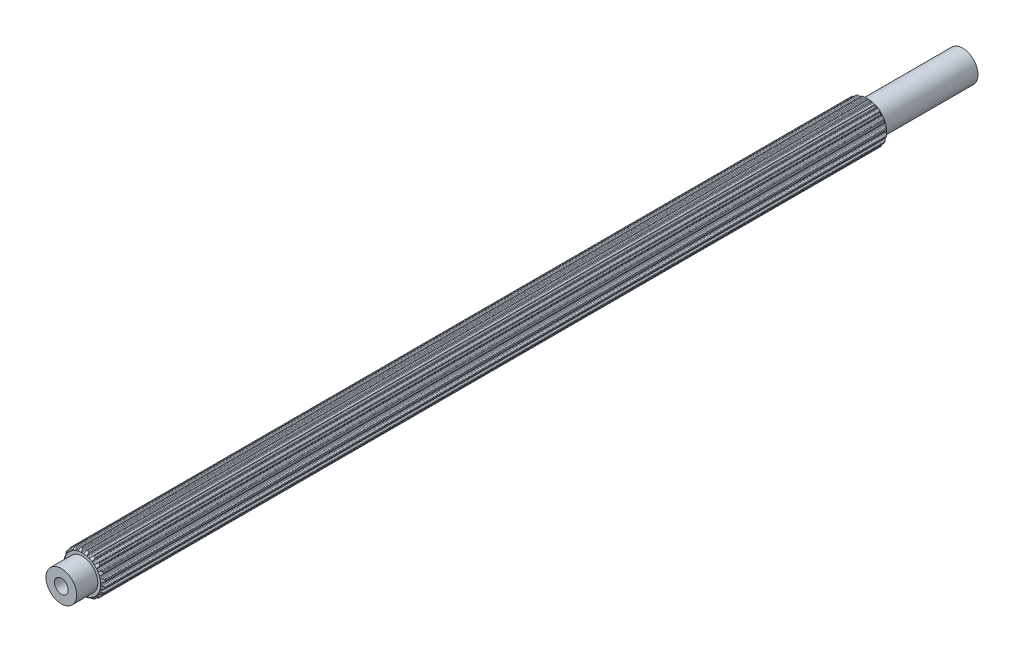
SolidWorks part; units mm, degrees
ref_plane "Front Plane" through (0, 0, 0) normal (0, 0, 1) x (1, 0, 0)
ref_plane "Top Plane" through (0, 0, 0) normal (0, 1, 0) x (1, 0, 0)
ref_plane "Right Plane" through (0, 0, 0) normal (1, 0, 0) x (0, 0, -1)
sketch "Sketch1" plane through (0, 0, 0) normal (0, 0, 1) x (1, 0, 0)
  line L0 (-0.1069, 2.9699) -> (0.1069, 2.9699)
  line L1 (0.3159, 3.2375) -> (0.2537, 3.0575)
  line L2 (-0.2964, 3.2367) -> (-0.2318, 3.0575)
  line L3 (-0.2964, 3.2367) -> (0.3159, 3.2375) construction
  line L4 (0, 3.3252) -> (0, 0) construction
  line L5 (-0.2318, 3.0575) -> (0.2537, 3.0575) construction
  line L6 (-0.4281, 3.3241) -> (0.4281, 3.3263) construction
  line L7 (0.7183, 3.1698) -> (0.7244, 2.9795)
  line L8 (0.816, 2.8576) -> (1.0195, 2.7915)
  line L9 (1.3009, 2.9815) -> (1.1862, 2.8295)
  line L10 (1.6627, 2.7927) -> (1.6097, 2.6099)
  line L11 (1.6591, 2.4655) -> (1.8322, 2.3398)
  line L12 (2.1585, 2.4335) -> (2.0025, 2.3245)
  line L13 (2.4443, 2.1423) -> (2.3374, 1.9847)
  line L14 (2.3398, 1.8322) -> (2.4655, 1.6591)
  line L15 (2.8049, 1.6474) -> (2.6228, 1.5919)
  line L16 (2.9866, 1.2821) -> (2.8363, 1.1653)
  line L17 (2.7915, 1.0195) -> (2.8576, 0.816)
  line L18 (3.1767, 0.7) -> (2.9863, 0.7035)
  line L19 (3.2367, 0.2964) -> (3.0575, 0.2318)
  line L20 (2.9699, 0.1069) -> (2.9699, -0.1069)
  line L21 (3.2375, -0.3159) -> (3.0575, -0.2537)
  line L22 (3.1698, -0.7183) -> (2.9795, -0.7244)
  line L23 (2.8576, -0.816) -> (2.7915, -1.0195)
  line L24 (2.9815, -1.3009) -> (2.8295, -1.1862)
  line L25 (2.7927, -1.6627) -> (2.6099, -1.6097)
  line L26 (2.4655, -1.6591) -> (2.3398, -1.8322)
  line L27 (2.4335, -2.1585) -> (2.3245, -2.0025)
  line L28 (2.1423, -2.4443) -> (1.9847, -2.3374)
  line L29 (1.8322, -2.3398) -> (1.6591, -2.4655)
  line L30 (1.6474, -2.8049) -> (1.5919, -2.6228)
  line L31 (1.2821, -2.9866) -> (1.1653, -2.8363)
  line L32 (1.0195, -2.7915) -> (0.816, -2.8576)
  line L33 (0.7, -3.1767) -> (0.7035, -2.9863)
  line L34 (0.2964, -3.2367) -> (0.2318, -3.0575)
  line L35 (0.1069, -2.9699) -> (-0.1069, -2.9699)
  line L36 (-0.3159, -3.2375) -> (-0.2537, -3.0575)
  line L37 (-0.7183, -3.1698) -> (-0.7244, -2.9795)
  line L38 (-0.816, -2.8576) -> (-1.0195, -2.7915)
  line L39 (-1.3009, -2.9815) -> (-1.1862, -2.8295)
  line L40 (-1.6627, -2.7927) -> (-1.6097, -2.6099)
  line L41 (-1.6591, -2.4655) -> (-1.8322, -2.3398)
  line L42 (-2.1585, -2.4335) -> (-2.0025, -2.3245)
  line L43 (-2.4443, -2.1423) -> (-2.3374, -1.9847)
  line L44 (-2.3398, -1.8322) -> (-2.4655, -1.6591)
  line L45 (-2.8049, -1.6474) -> (-2.6228, -1.5919)
  line L46 (-2.9866, -1.2821) -> (-2.8363, -1.1653)
  line L47 (-2.7915, -1.0195) -> (-2.8576, -0.816)
  line L48 (-3.1767, -0.7) -> (-2.9863, -0.7035)
  line L49 (-3.2367, -0.2964) -> (-3.0575, -0.2318)
  line L50 (-2.9699, -0.1069) -> (-2.9699, 0.1069)
  line L51 (-3.2375, 0.3159) -> (-3.0575, 0.2537)
  line L52 (-3.1698, 0.7183) -> (-2.9795, 0.7244)
  line L53 (-2.8576, 0.816) -> (-2.7915, 1.0195)
  line L54 (-2.9815, 1.3009) -> (-2.8295, 1.1862)
  line L55 (-2.7927, 1.6627) -> (-2.6099, 1.6097)
  line L56 (-2.4655, 1.6591) -> (-2.3398, 1.8322)
  line L57 (-2.4335, 2.1585) -> (-2.3245, 2.0025)
  line L58 (-2.1423, 2.4443) -> (-1.9847, 2.3374)
  line L59 (-1.8322, 2.3398) -> (-1.6591, 2.4655)
  line L60 (-1.6474, 2.8049) -> (-1.5919, 2.6228)
  line L61 (-1.2821, 2.9866) -> (-1.1653, 2.8363)
  line L62 (-1.0195, 2.7915) -> (-0.816, 2.8576)
  line L63 (-0.7, 3.1767) -> (-0.7035, 2.9863)
  line L64 (0.4281, 3.3263) -> (0.62, 3.2938)
  line L65 (1.4351, 3.0312) -> (1.6075, 2.9409)
  line L66 (2.3015, 2.4394) -> (2.4376, 2.3003)
  line L67 (2.9427, 1.6088) -> (3.0291, 1.4344)
  line L68 (3.2958, 0.6207) -> (3.3241, 0.4281)
  line L69 (3.3263, -0.4281) -> (3.2938, -0.62)
  line L70 (3.0312, -1.4351) -> (2.9409, -1.6075)
  line L71 (2.4394, -2.3015) -> (2.3003, -2.4376)
  line L72 (1.6088, -2.9427) -> (1.4344, -3.0291)
  line L73 (0.6207, -3.2958) -> (0.4281, -3.3241)
  line L74 (-0.4281, -3.3263) -> (-0.62, -3.2938)
  line L75 (-1.4351, -3.0312) -> (-1.6075, -2.9409)
  line L76 (-2.3015, -2.4394) -> (-2.4376, -2.3003)
  line L77 (-2.9427, -1.6088) -> (-3.0291, -1.4344)
  line L78 (-3.2958, -0.6207) -> (-3.3241, -0.4281)
  line L79 (-3.3263, 0.4281) -> (-3.2938, 0.62)
  line L80 (-3.0312, 1.4351) -> (-2.9409, 1.6075)
  line L81 (-2.4394, 2.3015) -> (-2.3003, 2.4376)
  line L82 (-1.6088, 2.9427) -> (-1.4344, 3.0291)
  line L83 (-0.6207, 3.2958) -> (-0.4281, 3.3241)
  arc A0 (0.2537, 3.0575) -> (0.1069, 2.9699) centre (0.1283, 3.1009) cw
  arc A1 (-0.2318, 3.0575) -> (-0.1069, 2.9699) centre (-0.1069, 3.1026) ccw
  arc A2 (0.62, 3.2938) -> (0.7183, 3.1698) centre (0.5856, 3.1656) cw
  arc A3 (0.7244, 2.9795) -> (0.816, 2.8576) centre (0.857, 2.9838) ccw
  arc A4 (-0.4281, 3.3241) -> (-0.2964, 3.2367) centre (-0.4213, 3.1916) cw
  arc A5 (0.4281, 3.3263) -> (0.3159, 3.2375) centre (0.4413, 3.1942) ccw
  arc A6 (1.1862, 2.8295) -> (1.0195, 2.7915) centre (1.0802, 2.9095) cw
  arc A7 (1.4351, 3.0312) -> (1.3009, 2.9815) centre (1.4068, 2.9015) ccw
  arc A8 (1.6075, 2.9409) -> (1.6627, 2.7927) centre (1.5352, 2.8297) cw
  arc A9 (1.6097, 2.6099) -> (1.6591, 2.4655) centre (1.7371, 2.5729) ccw
  arc A10 (2.0025, 2.3245) -> (1.8322, 2.3398) centre (1.9264, 2.4332) cw
  arc A11 (2.3015, 2.4394) -> (2.1585, 2.4335) centre (2.2346, 2.3248) ccw
  arc A12 (2.4376, 2.3003) -> (2.4443, 2.1423) centre (2.3345, 2.2168) cw
  arc A13 (2.3374, 1.9847) -> (2.3398, 1.8322) centre (2.4472, 1.9102) ccw
  arc A14 (2.6228, 1.5919) -> (2.4655, 1.6591) centre (2.5841, 1.7189) cw
  arc A15 (2.9427, 1.6088) -> (2.8049, 1.6474) centre (2.8436, 1.5205) ccw
  arc A16 (3.0291, 1.4344) -> (2.9866, 1.2821) centre (2.9052, 1.3869) cw
  arc A17 (2.8363, 1.1653) -> (2.7915, 1.0195) centre (2.9177, 1.0605) ccw
  arc A18 (2.9863, 0.7035) -> (2.8576, 0.816) centre (2.9887, 0.8362) cw
  arc A19 (3.2958, 0.6207) -> (3.1767, 0.7) centre (3.1743, 0.5673) ccw
  arc A20 (3.3241, 0.4281) -> (3.2367, 0.2964) centre (3.1916, 0.4213) cw
  arc A21 (3.0575, 0.2318) -> (2.9699, 0.1069) centre (3.1026, 0.1069) ccw
  arc A22 (3.0575, -0.2537) -> (2.9699, -0.1069) centre (3.1009, -0.1283) cw
  arc A23 (3.3263, -0.4281) -> (3.2375, -0.3159) centre (3.1942, -0.4413) ccw
  arc A24 (3.2938, -0.62) -> (3.1698, -0.7183) centre (3.1656, -0.5856) cw
  arc A25 (2.9795, -0.7244) -> (2.8576, -0.816) centre (2.9838, -0.857) ccw
  arc A26 (2.8295, -1.1862) -> (2.7915, -1.0195) centre (2.9095, -1.0802) cw
  arc A27 (3.0312, -1.4351) -> (2.9815, -1.3009) centre (2.9015, -1.4068) ccw
  arc A28 (2.9409, -1.6075) -> (2.7927, -1.6627) centre (2.8297, -1.5352) cw
  arc A29 (2.6099, -1.6097) -> (2.4655, -1.6591) centre (2.5729, -1.7371) ccw
  arc A30 (2.3245, -2.0025) -> (2.3398, -1.8322) centre (2.4332, -1.9264) cw
  arc A31 (2.4394, -2.3015) -> (2.4335, -2.1585) centre (2.3248, -2.2346) ccw
  arc A32 (2.3003, -2.4376) -> (2.1423, -2.4443) centre (2.2168, -2.3345) cw
  arc A33 (1.9847, -2.3374) -> (1.8322, -2.3398) centre (1.9102, -2.4472) ccw
  arc A34 (1.5919, -2.6228) -> (1.6591, -2.4655) centre (1.7189, -2.5841) cw
  arc A35 (1.6088, -2.9427) -> (1.6474, -2.8049) centre (1.5205, -2.8436) ccw
  arc A36 (1.4344, -3.0291) -> (1.2821, -2.9866) centre (1.3869, -2.9052) cw
  arc A37 (1.1653, -2.8363) -> (1.0195, -2.7915) centre (1.0605, -2.9177) ccw
  arc A38 (0.7035, -2.9863) -> (0.816, -2.8576) centre (0.8362, -2.9887) cw
  arc A39 (0.6207, -3.2958) -> (0.7, -3.1767) centre (0.5673, -3.1743) ccw
  arc A40 (0.4281, -3.3241) -> (0.2964, -3.2367) centre (0.4213, -3.1916) cw
  arc A41 (0.2318, -3.0575) -> (0.1069, -2.9699) centre (0.1069, -3.1026) ccw
  arc A42 (-0.2537, -3.0575) -> (-0.1069, -2.9699) centre (-0.1283, -3.1009) cw
  arc A43 (-0.4281, -3.3263) -> (-0.3159, -3.2375) centre (-0.4413, -3.1942) ccw
  arc A44 (-0.62, -3.2938) -> (-0.7183, -3.1698) centre (-0.5856, -3.1656) cw
  arc A45 (-0.7244, -2.9795) -> (-0.816, -2.8576) centre (-0.857, -2.9838) ccw
  arc A46 (-1.1862, -2.8295) -> (-1.0195, -2.7915) centre (-1.0802, -2.9095) cw
  arc A47 (-1.4351, -3.0312) -> (-1.3009, -2.9815) centre (-1.4068, -2.9015) ccw
  arc A48 (-1.6075, -2.9409) -> (-1.6627, -2.7927) centre (-1.5352, -2.8297) cw
  arc A49 (-1.6097, -2.6099) -> (-1.6591, -2.4655) centre (-1.7371, -2.5729) ccw
  arc A50 (-2.0025, -2.3245) -> (-1.8322, -2.3398) centre (-1.9264, -2.4332) cw
  arc A51 (-2.3015, -2.4394) -> (-2.1585, -2.4335) centre (-2.2346, -2.3248) ccw
  arc A52 (-2.4376, -2.3003) -> (-2.4443, -2.1423) centre (-2.3345, -2.2168) cw
  arc A53 (-2.3374, -1.9847) -> (-2.3398, -1.8322) centre (-2.4472, -1.9102) ccw
  arc A54 (-2.6228, -1.5919) -> (-2.4655, -1.6591) centre (-2.5841, -1.7189) cw
  arc A55 (-2.9427, -1.6088) -> (-2.8049, -1.6474) centre (-2.8436, -1.5205) ccw
  arc A56 (-3.0291, -1.4344) -> (-2.9866, -1.2821) centre (-2.9052, -1.3869) cw
  arc A57 (-2.8363, -1.1653) -> (-2.7915, -1.0195) centre (-2.9177, -1.0605) ccw
  arc A58 (-2.9863, -0.7035) -> (-2.8576, -0.816) centre (-2.9887, -0.8362) cw
  arc A59 (-3.2958, -0.6207) -> (-3.1767, -0.7) centre (-3.1743, -0.5673) ccw
  arc A60 (-3.3241, -0.4281) -> (-3.2367, -0.2964) centre (-3.1916, -0.4213) cw
  arc A61 (-3.0575, -0.2318) -> (-2.9699, -0.1069) centre (-3.1026, -0.1069) ccw
  arc A62 (-3.0575, 0.2537) -> (-2.9699, 0.1069) centre (-3.1009, 0.1283) cw
  arc A63 (-3.3263, 0.4281) -> (-3.2375, 0.3159) centre (-3.1942, 0.4413) ccw
  arc A64 (-3.2938, 0.62) -> (-3.1698, 0.7183) centre (-3.1656, 0.5856) cw
  arc A65 (-2.9795, 0.7244) -> (-2.8576, 0.816) centre (-2.9838, 0.857) ccw
  arc A66 (-2.8295, 1.1862) -> (-2.7915, 1.0195) centre (-2.9095, 1.0802) cw
  arc A67 (-3.0312, 1.4351) -> (-2.9815, 1.3009) centre (-2.9015, 1.4068) ccw
  arc A68 (-2.9409, 1.6075) -> (-2.7927, 1.6627) centre (-2.8297, 1.5352) cw
  arc A69 (-2.6099, 1.6097) -> (-2.4655, 1.6591) centre (-2.5729, 1.7371) ccw
  arc A70 (-2.3245, 2.0025) -> (-2.3398, 1.8322) centre (-2.4332, 1.9264) cw
  arc A71 (-2.4394, 2.3015) -> (-2.4335, 2.1585) centre (-2.3248, 2.2346) ccw
  arc A72 (-2.3003, 2.4376) -> (-2.1423, 2.4443) centre (-2.2168, 2.3345) cw
  arc A73 (-1.9847, 2.3374) -> (-1.8322, 2.3398) centre (-1.9102, 2.4472) ccw
  arc A74 (-1.5919, 2.6228) -> (-1.6591, 2.4655) centre (-1.7189, 2.5841) cw
  arc A75 (-1.6088, 2.9427) -> (-1.6474, 2.8049) centre (-1.5205, 2.8436) ccw
  arc A76 (-1.4344, 3.0291) -> (-1.2821, 2.9866) centre (-1.3869, 2.9052) cw
  arc A77 (-1.1653, 2.8363) -> (-1.0195, 2.7915) centre (-1.0605, 2.9177) ccw
  arc A78 (-0.7035, 2.9863) -> (-0.816, 2.8576) centre (-0.8362, 2.9887) cw
  arc A79 (-0.6207, 3.2958) -> (-0.7, 3.1767) centre (-0.5673, 3.1743) ccw
  point P14 (0, 2.9699)
  point P247 (0, 0)
  dimension "D4" = 0.1327
  dimension "D8" = 20
  dimension "D1" = 2.9699
  dimension "D2" = 0.2139
  dimension "D3" = 0.1904
  dimension "D5" = 0.0877
  dimension "D6" = 0.4855
  dimension "D7" = 0.8563
extrude "Boss-Extrude1" add sketch "Sketch1" along normal blind 70.0786 and the other way blind 58.1406
sketch "Sketch2" plane through (0, 0, 0) normal (0, 0, 1) x (1, 0, 0)
  circle A0 centre (0, 0) radius 2.5019
  dimension "D1" = 5.0038
extrude "Boss-Extrude2" add sketch "Sketch2" along normal mid plane 147.066
sketch "Sketch4" plane through (0, 0, 73.533) normal (0, 0, 1) x (1, 0, 0)
  circle A0 centre (0, 0) radius 2.5019 construction
  point P0 (0, 0)
sketch "Sketch5" plane through (0, 0, -73.533) normal (0, 0, -1) x (-1, 0, 0)
  circle A0 centre (0, 0) radius 2.5019 construction
  point P0 (0, 0)
sketch "Sketch3" plane through (0, 0, 0) normal (1, 0, 0) x (0, 0, -1)
  line L0 (-68.9474, 4.1011) -> (-70.0786, 2.9699)
  line L1 (-70.0786, 2.9699) -> (-70.0786, 4.1011)
  line L2 (-70.0786, 4.1011) -> (-68.9474, 4.1011)
  line L3 (-70.0786, 2.5019) -> (-70.0786, -2.5019) construction
  line L5 (-14.3608, 0) -> (13.2171, 0) construction
  line L7 (58.1406, 54.8545) -> (58.1406, 2.9699)
  line L8 (58.1406, 2.9699) -> (32.1983, 28.9122)
  line L9 (32.1983, 28.9122) -> (58.1406, 54.8545)
  line L10 (58.1406, -2.5019) -> (58.1406, 2.5019) construction
  point P6 (-4.866, 6.1438)
  dimension "D1" = 45
  dimension "D2" = 45
revolve "Cut-Revolve1" cut sketch "Sketch3" angle 360 about L5
sketch "Sketch6" plane through (0, 0, 0) normal (0, 0, 1) x (1, 0, 0)
  circle A0 centre (0, 0) radius 1.1303
  point P2 (12.3187, -9.1866)
  dimension "D1" = 2.2606
extrude "Cut-Extrude1" cut sketch "Sketch6" along normal up to surface and the other way up to surface up to face at (2.5019, 0, 73.533) other way up to face at (2.5019, 0, -73.533)
sketch "Sketch7" plane through (0, 0, 0) normal (0, 0, 1) x (1, 0, 0)
  circle A0 centre (0, 0) radius 1.1303
  circle A1 centre (0, 0) radius 1.1303 construction
  point P2 (5.7572, -5.7138)
extrude "Boss-Extrude3" add sketch "Sketch7" along normal offset from surface 9.525 and the other way offset from surface (64.008 mm away) 9.525 up to face at (1.1303, 0, 73.533) other way up to face at (1.1303, 0, -73.533)
